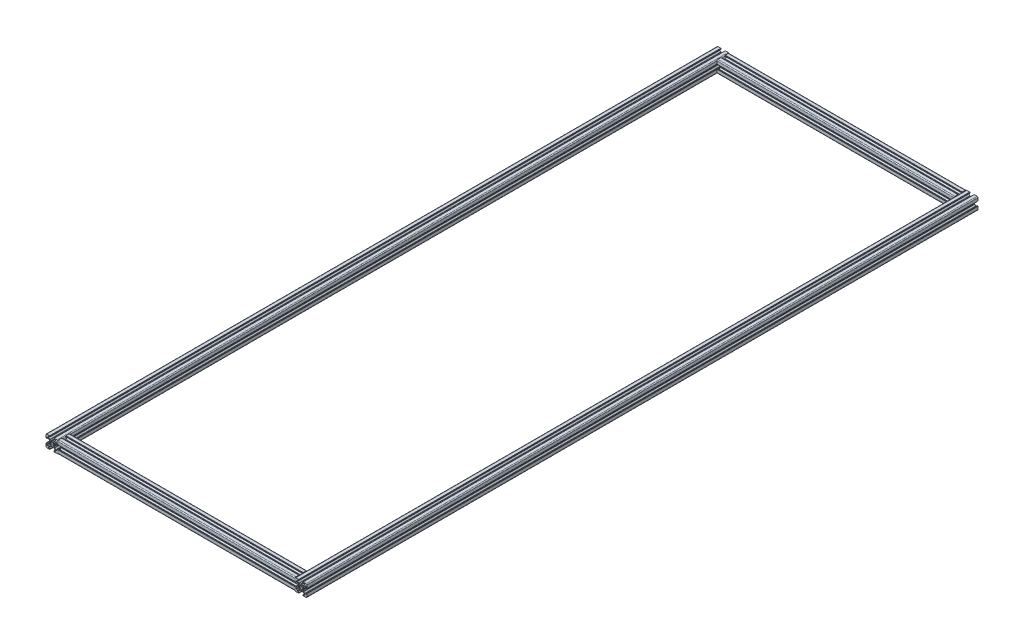
SolidWorks part; units mm, degrees
material "1060 Alloy"
ref_plane "Front Plane" through (0, 0, 0) normal (0, 0, 1) x (1, 0, 0)
ref_plane "Top Plane" through (0, 0, 0) normal (0, 1, 0) x (1, 0, 0)
ref_plane "Right Plane" through (0, 0, 0) normal (1, 0, 0) x (0, 0, -1)
sketch "Sketch1" plane through (0, 0, 0) normal (0, 1, 0) x (1, 0, 0)
  line L0 (0, -491.0294) -> (0, 633.9706)
  line L2 (417.4, -491.0294) -> (417.4, 633.9706)
  dimension "D1" = 1125
  dimension "D2" = 417.4
other "T-slot 20X20(1)"
ref_plane "Plane1" through (0, 0, 491.0294) normal (0, 0, -1) x (-1, 0, 0)
sketch "Sketch11" plane through (0, 0, 491.0294) normal (0, 0, -1) x (-1, 0, 0)
  line L0 (2.9914, 1.9095) -> (2.4445, 1.2578)
  line L1 (2.4445, -1.2578) -> (2.9914, -1.9095)
  line L2 (1.9134, -2.9889) -> (1.2578, -2.4445)
  line L3 (-1.2578, -2.4445) -> (-1.9135, -2.9889)
  line L4 (-2.9914, -1.9095) -> (-2.4445, -1.2578)
  line L5 (-2.4445, 1.2578) -> (-2.9914, 1.9095)
  line L6 (-1.9134, 2.9889) -> (-1.2578, 2.4445)
  line L7 (1.2577, 2.4446) -> (1.9134, 2.9889)
  line L8 (5.4998, -8.4985) -> (3.4998, -8.4985)
  line L9 (2.9998, -8.9985) -> (2.9998, -9.2985)
  line L10 (3.1998, -9.4985) -> (3.3489, -9.4985)
  line L11 (3.5489, -9.6985) -> (3.5489, -9.7989)
  line L12 (3.7489, -9.9989) -> (8.5002, -9.9989)
  line L13 (10.0002, -8.4989) -> (10.0002, -3.7489)
  line L14 (9.8002, -3.5489) -> (9.6994, -3.5489)
  line L15 (9.4994, -3.3489) -> (9.4994, -3.1985)
  line L16 (9.2994, -2.9985) -> (8.9994, -2.9985)
  line L17 (8.4994, -3.4985) -> (8.4994, -5.4986)
  line L18 (7.9994, -5.9986) -> (7.2672, -5.9986)
  line L19 (6.9136, -5.8521) -> (4.6458, -3.5844)
  line L20 (4.4994, -3.2308) -> (4.4994, -0.9522)
  line L21 (4.4726, -0.8522) -> (4.0375, -0.0986)
  line L22 (4.0375, 0.1014) -> (4.4726, 0.855)
  line L23 (4.4994, 0.955) -> (4.4994, 3.2333)
  line L24 (4.6458, 3.5869) -> (6.9136, 5.8546)
  line L25 (7.2672, 6.0011) -> (7.9994, 6.0011)
  line L26 (8.4994, 5.5011) -> (8.4994, 3.5007)
  line L27 (8.9994, 3.0007) -> (9.2994, 3.0007)
  line L28 (9.4994, 3.2007) -> (9.4994, 3.3489)
  line L29 (9.6994, 3.5489) -> (9.8002, 3.5489)
  line L30 (10.0002, 3.7489) -> (10.0002, 8.4989)
  line L31 (8.5002, 9.9989) -> (3.7489, 9.9989)
  line L32 (3.5489, 9.7989) -> (3.5489, 9.7011)
  line L33 (3.3489, 9.5011) -> (3.1998, 9.5011)
  line L34 (2.9998, 9.3011) -> (2.9998, 9.0011)
  line L35 (3.4998, 8.5011) -> (5.4998, 8.5011)
  line L36 (5.9998, 8.0011) -> (5.9998, 7.2692)
  line L37 (5.8533, 6.9156) -> (3.5852, 4.6475)
  line L38 (3.2317, 4.5011) -> (0.953, 4.5011)
  line L39 (0.853, 4.4743) -> (0.0994, 4.0392)
  line L40 (-0.1006, 4.0392) -> (-0.8542, 4.4743)
  line L41 (-0.9542, 4.5011) -> (-3.2325, 4.5011)
  line L42 (-3.586, 4.6475) -> (-5.8541, 6.9157)
  line L43 (-6.0006, 7.2692) -> (-6.0006, 8.0011)
  line L44 (-5.5006, 8.5011) -> (-3.5002, 8.5011)
  line L45 (-3.0002, 9.0011) -> (-3.0002, 9.3011)
  line L46 (-3.2002, 9.5011) -> (-3.3489, 9.5011)
  line L47 (-3.5489, 9.7011) -> (-3.5489, 9.7989)
  line L48 (-3.7489, 9.9989) -> (-8.4985, 9.9989)
  line L49 (-9.9985, 8.4989) -> (-9.9985, 3.7489)
  line L50 (-9.7985, 3.5489) -> (-9.6999, 3.5489)
  line L51 (-9.4999, 3.3489) -> (-9.4999, 3.2007)
  line L52 (-9.2999, 3.0007) -> (-8.9999, 3.0007)
  line L53 (-8.4999, 3.5007) -> (-8.4999, 5.5011)
  line L54 (-7.9999, 6.0011) -> (-7.2679, 6.0011)
  line L55 (-6.9144, 5.8546) -> (-4.6467, 3.5869)
  line L56 (-4.5003, 3.2334) -> (-4.5003, 0.955)
  line L57 (-4.4735, 0.855) -> (-4.0384, 0.1014)
  line L58 (-4.0384, -0.0986) -> (-4.4735, -0.8522)
  line L59 (-4.5003, -0.9522) -> (-4.5003, -3.2308)
  line L60 (-4.6467, -3.5844) -> (-6.9145, -5.8521)
  line L61 (-7.268, -5.9986) -> (-7.9999, -5.9986)
  line L62 (-8.4999, -5.4986) -> (-8.4999, -3.4985)
  line L63 (-8.9999, -2.9985) -> (-9.2999, -2.9985)
  line L64 (-9.4999, -3.1985) -> (-9.4999, -3.3489)
  line L65 (-9.6999, -3.5489) -> (-9.7985, -3.5489)
  line L66 (-9.9985, -3.7489) -> (-9.9985, -8.4989)
  line L67 (-8.4985, -9.9989) -> (-3.7489, -9.9989)
  line L68 (-3.5489, -9.7989) -> (-3.5489, -9.6985)
  line L69 (-3.3489, -9.4985) -> (-3.2002, -9.4985)
  line L70 (-3.0002, -9.2985) -> (-3.0002, -8.9985)
  line L71 (-3.5002, -8.4985) -> (-5.5006, -8.4985)
  line L72 (-6.0006, -7.9985) -> (-6.0006, -7.2667)
  line L73 (-5.8541, -6.9131) -> (-3.5864, -4.6454)
  line L74 (-3.2328, -4.4989) -> (-0.9542, -4.4989)
  line L75 (-0.8542, -4.4721) -> (-0.1006, -4.037)
  line L76 (0.0994, -4.037) -> (0.853, -4.4721)
  line L77 (0.953, -4.4989) -> (3.232, -4.4989)
  line L78 (3.5856, -4.6454) -> (5.8533, -6.9131)
  line L79 (5.9998, -7.2667) -> (5.9998, -7.9985)
  arc A0 (2.4445, 1.2578) -> (2.4445, -1.2578) centre (0, 0) cw
  arc A1 (2.9914, -1.9095) -> (1.9134, -2.9889) centre (0, 0) cw
  arc A2 (1.2578, -2.4445) -> (-1.2578, -2.4445) centre (0, 0) cw
  arc A3 (-1.9135, -2.9889) -> (-2.9914, -1.9095) centre (0, 0) cw
  arc A4 (-2.4445, -1.2578) -> (-2.4445, 1.2578) centre (0, 0) cw
  arc A5 (-2.9914, 1.9095) -> (-1.9134, 2.9889) centre (0, 0) cw
  arc A6 (-1.2578, 2.4445) -> (1.2577, 2.4446) centre (0, 0) cw
  arc A7 (1.9134, 2.9889) -> (2.9914, 1.9095) centre (0, 0) cw
  arc A8 (5.9998, -7.9985) -> (5.4998, -8.4985) centre (5.4998, -7.9985) cw
  arc A9 (3.4998, -8.4985) -> (2.9998, -8.9985) centre (3.4998, -8.9985) ccw
  arc A10 (2.9998, -9.2985) -> (3.1998, -9.4985) centre (3.1998, -9.2985) ccw
  arc A11 (3.3489, -9.4985) -> (3.5489, -9.6985) centre (3.3489, -9.6985) cw
  arc A12 (3.5489, -9.7989) -> (3.7489, -9.9989) centre (3.7489, -9.7989) ccw
  arc A13 (8.5002, -9.9989) -> (10.0002, -8.4989) centre (8.5002, -8.4989) ccw
  arc A14 (10.0002, -3.7489) -> (9.8002, -3.5489) centre (9.8002, -3.7489) ccw
  arc A15 (9.6994, -3.5489) -> (9.4994, -3.3489) centre (9.6994, -3.3489) cw
  arc A16 (9.4994, -3.1985) -> (9.2994, -2.9985) centre (9.2994, -3.1985) ccw
  arc A17 (8.9994, -2.9985) -> (8.4994, -3.4985) centre (8.9994, -3.4985) ccw
  arc A18 (8.4994, -5.4986) -> (7.9994, -5.9986) centre (7.9994, -5.4986) cw
  arc A19 (7.2672, -5.9986) -> (6.9136, -5.8521) centre (7.2672, -5.4986) cw
  arc A20 (4.6458, -3.5844) -> (4.4994, -3.2308) centre (4.9994, -3.2308) cw
  arc A21 (4.4994, -0.9522) -> (4.4726, -0.8522) centre (4.2994, -0.9522) ccw
  arc A22 (4.0375, -0.0986) -> (4.0375, 0.1014) centre (4.2107, 0.0014) cw
  arc A23 (4.4726, 0.855) -> (4.4994, 0.955) centre (4.2994, 0.955) ccw
  arc A24 (4.4994, 3.2333) -> (4.6458, 3.5869) centre (4.9994, 3.2333) cw
  arc A25 (6.9136, 5.8546) -> (7.2672, 6.0011) centre (7.2672, 5.5011) cw
  arc A26 (7.9994, 6.0011) -> (8.4994, 5.5011) centre (7.9994, 5.5011) cw
  arc A27 (8.4994, 3.5007) -> (8.9994, 3.0007) centre (8.9994, 3.5007) ccw
  arc A28 (9.2994, 3.0007) -> (9.4994, 3.2007) centre (9.2994, 3.2007) ccw
  arc A29 (9.4994, 3.3489) -> (9.6994, 3.5489) centre (9.6994, 3.3489) cw
  arc A30 (9.8002, 3.5489) -> (10.0002, 3.7489) centre (9.8002, 3.7489) ccw
  arc A31 (10.0002, 8.4989) -> (8.5002, 9.9989) centre (8.5002, 8.4989) ccw
  arc A32 (3.7489, 9.9989) -> (3.5489, 9.7989) centre (3.7489, 9.7989) ccw
  arc A33 (3.5489, 9.7011) -> (3.3489, 9.5011) centre (3.3489, 9.7011) cw
  arc A34 (3.1998, 9.5011) -> (2.9998, 9.3011) centre (3.1998, 9.3011) ccw
  arc A35 (2.9998, 9.0011) -> (3.4998, 8.5011) centre (3.4998, 9.0011) ccw
  arc A36 (5.4998, 8.5011) -> (5.9998, 8.0011) centre (5.4998, 8.0011) cw
  arc A37 (5.9998, 7.2692) -> (5.8533, 6.9156) centre (5.4998, 7.2692) cw
  arc A38 (3.5852, 4.6475) -> (3.2317, 4.5011) centre (3.2317, 5.0011) cw
  arc A39 (0.953, 4.5011) -> (0.853, 4.4743) centre (0.953, 4.3011) ccw
  arc A40 (0.0994, 4.0392) -> (-0.1006, 4.0392) centre (-0.0006, 4.2124) cw
  arc A41 (-0.8542, 4.4743) -> (-0.9542, 4.5011) centre (-0.9542, 4.3011) ccw
  arc A42 (-3.2325, 4.5011) -> (-3.586, 4.6475) centre (-3.2325, 5.0011) cw
  arc A43 (-5.8541, 6.9157) -> (-6.0006, 7.2692) centre (-5.5006, 7.2692) cw
  arc A44 (-6.0006, 8.0011) -> (-5.5006, 8.5011) centre (-5.5006, 8.0011) cw
  arc A45 (-3.5002, 8.5011) -> (-3.0002, 9.0011) centre (-3.5002, 9.0011) ccw
  arc A46 (-3.0002, 9.3011) -> (-3.2002, 9.5011) centre (-3.2002, 9.3011) ccw
  arc A47 (-3.3489, 9.5011) -> (-3.5489, 9.7011) centre (-3.3489, 9.7011) cw
  arc A48 (-3.5489, 9.7989) -> (-3.7489, 9.9989) centre (-3.7489, 9.7989) ccw
  arc A49 (-8.4985, 9.9989) -> (-9.9985, 8.4989) centre (-8.4985, 8.4989) ccw
  arc A50 (-9.9985, 3.7489) -> (-9.7985, 3.5489) centre (-9.7985, 3.7489) ccw
  arc A51 (-9.6999, 3.5489) -> (-9.4999, 3.3489) centre (-9.6999, 3.3489) cw
  arc A52 (-9.4999, 3.2007) -> (-9.2999, 3.0007) centre (-9.2999, 3.2007) ccw
  arc A53 (-8.9999, 3.0007) -> (-8.4999, 3.5007) centre (-8.9999, 3.5007) ccw
  arc A54 (-8.4999, 5.5011) -> (-7.9999, 6.0011) centre (-7.9999, 5.5011) cw
  arc A55 (-7.2679, 6.0011) -> (-6.9144, 5.8546) centre (-7.2679, 5.5011) cw
  arc A56 (-4.6467, 3.5869) -> (-4.5003, 3.2334) centre (-5.0003, 3.2334) cw
  arc A57 (-4.5003, 0.955) -> (-4.4735, 0.855) centre (-4.3003, 0.955) ccw
  arc A58 (-4.0384, 0.1014) -> (-4.0384, -0.0986) centre (-4.2116, 0.0014) cw
  arc A59 (-4.4735, -0.8522) -> (-4.5003, -0.9522) centre (-4.3003, -0.9522) ccw
  arc A60 (-4.5003, -3.2308) -> (-4.6467, -3.5844) centre (-5.0003, -3.2308) cw
  arc A61 (-6.9145, -5.8521) -> (-7.268, -5.9986) centre (-7.268, -5.4986) cw
  arc A62 (-7.9999, -5.9986) -> (-8.4999, -5.4986) centre (-7.9999, -5.4986) cw
  arc A63 (-8.4999, -3.4985) -> (-8.9999, -2.9985) centre (-8.9999, -3.4985) ccw
  arc A64 (-9.2999, -2.9985) -> (-9.4999, -3.1985) centre (-9.2999, -3.1985) ccw
  arc A65 (-9.4999, -3.3489) -> (-9.6999, -3.5489) centre (-9.6999, -3.3489) cw
  arc A66 (-9.7985, -3.5489) -> (-9.9985, -3.7489) centre (-9.7985, -3.7489) ccw
  arc A67 (-9.9985, -8.4989) -> (-8.4985, -9.9989) centre (-8.4985, -8.4989) ccw
  arc A68 (-3.7489, -9.9989) -> (-3.5489, -9.7989) centre (-3.7489, -9.7989) ccw
  arc A69 (-3.5489, -9.6985) -> (-3.3489, -9.4985) centre (-3.3489, -9.6985) cw
  arc A70 (-3.2002, -9.4985) -> (-3.0002, -9.2985) centre (-3.2002, -9.2985) ccw
  arc A71 (-3.0002, -8.9985) -> (-3.5002, -8.4985) centre (-3.5002, -8.9985) ccw
  arc A72 (-5.5006, -8.4985) -> (-6.0006, -7.9985) centre (-5.5006, -7.9985) cw
  arc A73 (-6.0006, -7.2667) -> (-5.8541, -6.9131) centre (-5.5006, -7.2667) cw
  arc A74 (-3.5864, -4.6454) -> (-3.2328, -4.4989) centre (-3.2328, -4.9989) cw
  arc A75 (-0.9542, -4.4989) -> (-0.8542, -4.4721) centre (-0.9542, -4.2989) ccw
  arc A76 (-0.1006, -4.037) -> (0.0994, -4.037) centre (-0.0006, -4.2102) cw
  arc A77 (0.853, -4.4721) -> (0.953, -4.4989) centre (0.953, -4.2989) ccw
  arc A78 (3.232, -4.4989) -> (3.5856, -4.6454) centre (3.232, -4.9989) cw
  arc A79 (5.8533, -6.9131) -> (5.9998, -7.2667) centre (5.4998, -7.2667) cw
  point P233 (0, 0)
sketch "Sketch12" plane through (0, 0, 0) normal (0, 1, 0) x (1, 0, 0)
  line L0 (9.9985, 633.9706) -> (9.9985, -491.0294) construction
  line L1 (9.9985, 623.9706) -> (407.3998, 623.9706)
  line L2 (407.3998, 633.9706) -> (407.3998, -491.0294) construction
  point P0 (9.9985, 623.9706)
  dimension "D1" = 10
other "T-slot 20X20(2)"
ref_plane "Plane2" through (9.9985, 0, -623.9706) normal (1, 0, 0) x (0, 0, -1)
sketch "Sketch13" plane through (9.9985, 0, -623.9706) normal (1, 0, 0) x (0, 0, -1)
  line L0 (2.9914, 1.9095) -> (2.4445, 1.2578)
  line L1 (2.4445, -1.2578) -> (2.9914, -1.9095)
  line L2 (1.9134, -2.9889) -> (1.2578, -2.4445)
  line L3 (-1.2578, -2.4445) -> (-1.9135, -2.9889)
  line L4 (-2.9914, -1.9095) -> (-2.4445, -1.2578)
  line L5 (-2.4445, 1.2578) -> (-2.9914, 1.9095)
  line L6 (-1.9134, 2.9889) -> (-1.2578, 2.4445)
  line L7 (1.2577, 2.4446) -> (1.9134, 2.9889)
  line L8 (5.4998, -8.4985) -> (3.4998, -8.4985)
  line L9 (2.9998, -8.9985) -> (2.9998, -9.2985)
  line L10 (3.1998, -9.4985) -> (3.3489, -9.4985)
  line L11 (3.5489, -9.6985) -> (3.5489, -9.7989)
  line L12 (3.7489, -9.9989) -> (8.5002, -9.9989)
  line L13 (10.0002, -8.4989) -> (10.0002, -3.7489)
  line L14 (9.8002, -3.5489) -> (9.6994, -3.5489)
  line L15 (9.4994, -3.3489) -> (9.4994, -3.1985)
  line L16 (9.2994, -2.9985) -> (8.9994, -2.9985)
  line L17 (8.4994, -3.4985) -> (8.4994, -5.4986)
  line L18 (7.9994, -5.9986) -> (7.2672, -5.9986)
  line L19 (6.9136, -5.8521) -> (4.6458, -3.5844)
  line L20 (4.4994, -3.2308) -> (4.4994, -0.9522)
  line L21 (4.4726, -0.8522) -> (4.0375, -0.0986)
  line L22 (4.0375, 0.1014) -> (4.4726, 0.855)
  line L23 (4.4994, 0.955) -> (4.4994, 3.2333)
  line L24 (4.6458, 3.5869) -> (6.9136, 5.8546)
  line L25 (7.2672, 6.0011) -> (7.9994, 6.0011)
  line L26 (8.4994, 5.5011) -> (8.4994, 3.5007)
  line L27 (8.9994, 3.0007) -> (9.2994, 3.0007)
  line L28 (9.4994, 3.2007) -> (9.4994, 3.3489)
  line L29 (9.6994, 3.5489) -> (9.8002, 3.5489)
  line L30 (10.0002, 3.7489) -> (10.0002, 8.4989)
  line L31 (8.5002, 9.9989) -> (3.7489, 9.9989)
  line L32 (3.5489, 9.7989) -> (3.5489, 9.7011)
  line L33 (3.3489, 9.5011) -> (3.1998, 9.5011)
  line L34 (2.9998, 9.3011) -> (2.9998, 9.0011)
  line L35 (3.4998, 8.5011) -> (5.4998, 8.5011)
  line L36 (5.9998, 8.0011) -> (5.9998, 7.2692)
  line L37 (5.8533, 6.9156) -> (3.5852, 4.6475)
  line L38 (3.2317, 4.5011) -> (0.953, 4.5011)
  line L39 (0.853, 4.4743) -> (0.0994, 4.0392)
  line L40 (-0.1006, 4.0392) -> (-0.8542, 4.4743)
  line L41 (-0.9542, 4.5011) -> (-3.2325, 4.5011)
  line L42 (-3.586, 4.6475) -> (-5.8541, 6.9157)
  line L43 (-6.0006, 7.2692) -> (-6.0006, 8.0011)
  line L44 (-5.5006, 8.5011) -> (-3.5002, 8.5011)
  line L45 (-3.0002, 9.0011) -> (-3.0002, 9.3011)
  line L46 (-3.2002, 9.5011) -> (-3.3489, 9.5011)
  line L47 (-3.5489, 9.7011) -> (-3.5489, 9.7989)
  line L48 (-3.7489, 9.9989) -> (-8.4985, 9.9989)
  line L49 (-9.9985, 8.4989) -> (-9.9985, 3.7489)
  line L50 (-9.7985, 3.5489) -> (-9.6999, 3.5489)
  line L51 (-9.4999, 3.3489) -> (-9.4999, 3.2007)
  line L52 (-9.2999, 3.0007) -> (-8.9999, 3.0007)
  line L53 (-8.4999, 3.5007) -> (-8.4999, 5.5011)
  line L54 (-7.9999, 6.0011) -> (-7.2679, 6.0011)
  line L55 (-6.9144, 5.8546) -> (-4.6467, 3.5869)
  line L56 (-4.5003, 3.2334) -> (-4.5003, 0.955)
  line L57 (-4.4735, 0.855) -> (-4.0384, 0.1014)
  line L58 (-4.0384, -0.0986) -> (-4.4735, -0.8522)
  line L59 (-4.5003, -0.9522) -> (-4.5003, -3.2308)
  line L60 (-4.6467, -3.5844) -> (-6.9145, -5.8521)
  line L61 (-7.268, -5.9986) -> (-7.9999, -5.9986)
  line L62 (-8.4999, -5.4986) -> (-8.4999, -3.4985)
  line L63 (-8.9999, -2.9985) -> (-9.2999, -2.9985)
  line L64 (-9.4999, -3.1985) -> (-9.4999, -3.3489)
  line L65 (-9.6999, -3.5489) -> (-9.7985, -3.5489)
  line L66 (-9.9985, -3.7489) -> (-9.9985, -8.4989)
  line L67 (-8.4985, -9.9989) -> (-3.7489, -9.9989)
  line L68 (-3.5489, -9.7989) -> (-3.5489, -9.6985)
  line L69 (-3.3489, -9.4985) -> (-3.2002, -9.4985)
  line L70 (-3.0002, -9.2985) -> (-3.0002, -8.9985)
  line L71 (-3.5002, -8.4985) -> (-5.5006, -8.4985)
  line L72 (-6.0006, -7.9985) -> (-6.0006, -7.2667)
  line L73 (-5.8541, -6.9131) -> (-3.5864, -4.6454)
  line L74 (-3.2328, -4.4989) -> (-0.9542, -4.4989)
  line L75 (-0.8542, -4.4721) -> (-0.1006, -4.037)
  line L76 (0.0994, -4.037) -> (0.853, -4.4721)
  line L77 (0.953, -4.4989) -> (3.232, -4.4989)
  line L78 (3.5856, -4.6454) -> (5.8533, -6.9131)
  line L79 (5.9998, -7.2667) -> (5.9998, -7.9985)
  arc A0 (2.4445, 1.2578) -> (2.4445, -1.2578) centre (0, 0) cw
  arc A1 (2.9914, -1.9095) -> (1.9134, -2.9889) centre (0, 0) cw
  arc A2 (1.2578, -2.4445) -> (-1.2578, -2.4445) centre (0, 0) cw
  arc A3 (-1.9135, -2.9889) -> (-2.9914, -1.9095) centre (0, 0) cw
  arc A4 (-2.4445, -1.2578) -> (-2.4445, 1.2578) centre (0, 0) cw
  arc A5 (-2.9914, 1.9095) -> (-1.9134, 2.9889) centre (0, 0) cw
  arc A6 (-1.2578, 2.4445) -> (1.2577, 2.4446) centre (0, 0) cw
  arc A7 (1.9134, 2.9889) -> (2.9914, 1.9095) centre (0, 0) cw
  arc A8 (5.9998, -7.9985) -> (5.4998, -8.4985) centre (5.4998, -7.9985) cw
  arc A9 (3.4998, -8.4985) -> (2.9998, -8.9985) centre (3.4998, -8.9985) ccw
  arc A10 (2.9998, -9.2985) -> (3.1998, -9.4985) centre (3.1998, -9.2985) ccw
  arc A11 (3.3489, -9.4985) -> (3.5489, -9.6985) centre (3.3489, -9.6985) cw
  arc A12 (3.5489, -9.7989) -> (3.7489, -9.9989) centre (3.7489, -9.7989) ccw
  arc A13 (8.5002, -9.9989) -> (10.0002, -8.4989) centre (8.5002, -8.4989) ccw
  arc A14 (10.0002, -3.7489) -> (9.8002, -3.5489) centre (9.8002, -3.7489) ccw
  arc A15 (9.6994, -3.5489) -> (9.4994, -3.3489) centre (9.6994, -3.3489) cw
  arc A16 (9.4994, -3.1985) -> (9.2994, -2.9985) centre (9.2994, -3.1985) ccw
  arc A17 (8.9994, -2.9985) -> (8.4994, -3.4985) centre (8.9994, -3.4985) ccw
  arc A18 (8.4994, -5.4986) -> (7.9994, -5.9986) centre (7.9994, -5.4986) cw
  arc A19 (7.2672, -5.9986) -> (6.9136, -5.8521) centre (7.2672, -5.4986) cw
  arc A20 (4.6458, -3.5844) -> (4.4994, -3.2308) centre (4.9994, -3.2308) cw
  arc A21 (4.4994, -0.9522) -> (4.4726, -0.8522) centre (4.2994, -0.9522) ccw
  arc A22 (4.0375, -0.0986) -> (4.0375, 0.1014) centre (4.2107, 0.0014) cw
  arc A23 (4.4726, 0.855) -> (4.4994, 0.955) centre (4.2994, 0.955) ccw
  arc A24 (4.4994, 3.2333) -> (4.6458, 3.5869) centre (4.9994, 3.2333) cw
  arc A25 (6.9136, 5.8546) -> (7.2672, 6.0011) centre (7.2672, 5.5011) cw
  arc A26 (7.9994, 6.0011) -> (8.4994, 5.5011) centre (7.9994, 5.5011) cw
  arc A27 (8.4994, 3.5007) -> (8.9994, 3.0007) centre (8.9994, 3.5007) ccw
  arc A28 (9.2994, 3.0007) -> (9.4994, 3.2007) centre (9.2994, 3.2007) ccw
  arc A29 (9.4994, 3.3489) -> (9.6994, 3.5489) centre (9.6994, 3.3489) cw
  arc A30 (9.8002, 3.5489) -> (10.0002, 3.7489) centre (9.8002, 3.7489) ccw
  arc A31 (10.0002, 8.4989) -> (8.5002, 9.9989) centre (8.5002, 8.4989) ccw
  arc A32 (3.7489, 9.9989) -> (3.5489, 9.7989) centre (3.7489, 9.7989) ccw
  arc A33 (3.5489, 9.7011) -> (3.3489, 9.5011) centre (3.3489, 9.7011) cw
  arc A34 (3.1998, 9.5011) -> (2.9998, 9.3011) centre (3.1998, 9.3011) ccw
  arc A35 (2.9998, 9.0011) -> (3.4998, 8.5011) centre (3.4998, 9.0011) ccw
  arc A36 (5.4998, 8.5011) -> (5.9998, 8.0011) centre (5.4998, 8.0011) cw
  arc A37 (5.9998, 7.2692) -> (5.8533, 6.9156) centre (5.4998, 7.2692) cw
  arc A38 (3.5852, 4.6475) -> (3.2317, 4.5011) centre (3.2317, 5.0011) cw
  arc A39 (0.953, 4.5011) -> (0.853, 4.4743) centre (0.953, 4.3011) ccw
  arc A40 (0.0994, 4.0392) -> (-0.1006, 4.0392) centre (-0.0006, 4.2124) cw
  arc A41 (-0.8542, 4.4743) -> (-0.9542, 4.5011) centre (-0.9542, 4.3011) ccw
  arc A42 (-3.2325, 4.5011) -> (-3.586, 4.6475) centre (-3.2325, 5.0011) cw
  arc A43 (-5.8541, 6.9157) -> (-6.0006, 7.2692) centre (-5.5006, 7.2692) cw
  arc A44 (-6.0006, 8.0011) -> (-5.5006, 8.5011) centre (-5.5006, 8.0011) cw
  arc A45 (-3.5002, 8.5011) -> (-3.0002, 9.0011) centre (-3.5002, 9.0011) ccw
  arc A46 (-3.0002, 9.3011) -> (-3.2002, 9.5011) centre (-3.2002, 9.3011) ccw
  arc A47 (-3.3489, 9.5011) -> (-3.5489, 9.7011) centre (-3.3489, 9.7011) cw
  arc A48 (-3.5489, 9.7989) -> (-3.7489, 9.9989) centre (-3.7489, 9.7989) ccw
  arc A49 (-8.4985, 9.9989) -> (-9.9985, 8.4989) centre (-8.4985, 8.4989) ccw
  arc A50 (-9.9985, 3.7489) -> (-9.7985, 3.5489) centre (-9.7985, 3.7489) ccw
  arc A51 (-9.6999, 3.5489) -> (-9.4999, 3.3489) centre (-9.6999, 3.3489) cw
  arc A52 (-9.4999, 3.2007) -> (-9.2999, 3.0007) centre (-9.2999, 3.2007) ccw
  arc A53 (-8.9999, 3.0007) -> (-8.4999, 3.5007) centre (-8.9999, 3.5007) ccw
  arc A54 (-8.4999, 5.5011) -> (-7.9999, 6.0011) centre (-7.9999, 5.5011) cw
  arc A55 (-7.2679, 6.0011) -> (-6.9144, 5.8546) centre (-7.2679, 5.5011) cw
  arc A56 (-4.6467, 3.5869) -> (-4.5003, 3.2334) centre (-5.0003, 3.2334) cw
  arc A57 (-4.5003, 0.955) -> (-4.4735, 0.855) centre (-4.3003, 0.955) ccw
  arc A58 (-4.0384, 0.1014) -> (-4.0384, -0.0986) centre (-4.2116, 0.0014) cw
  arc A59 (-4.4735, -0.8522) -> (-4.5003, -0.9522) centre (-4.3003, -0.9522) ccw
  arc A60 (-4.5003, -3.2308) -> (-4.6467, -3.5844) centre (-5.0003, -3.2308) cw
  arc A61 (-6.9145, -5.8521) -> (-7.268, -5.9986) centre (-7.268, -5.4986) cw
  arc A62 (-7.9999, -5.9986) -> (-8.4999, -5.4986) centre (-7.9999, -5.4986) cw
  arc A63 (-8.4999, -3.4985) -> (-8.9999, -2.9985) centre (-8.9999, -3.4985) ccw
  arc A64 (-9.2999, -2.9985) -> (-9.4999, -3.1985) centre (-9.2999, -3.1985) ccw
  arc A65 (-9.4999, -3.3489) -> (-9.6999, -3.5489) centre (-9.6999, -3.3489) cw
  arc A66 (-9.7985, -3.5489) -> (-9.9985, -3.7489) centre (-9.7985, -3.7489) ccw
  arc A67 (-9.9985, -8.4989) -> (-8.4985, -9.9989) centre (-8.4985, -8.4989) ccw
  arc A68 (-3.7489, -9.9989) -> (-3.5489, -9.7989) centre (-3.7489, -9.7989) ccw
  arc A69 (-3.5489, -9.6985) -> (-3.3489, -9.4985) centre (-3.3489, -9.6985) cw
  arc A70 (-3.2002, -9.4985) -> (-3.0002, -9.2985) centre (-3.2002, -9.2985) ccw
  arc A71 (-3.0002, -8.9985) -> (-3.5002, -8.4985) centre (-3.5002, -8.9985) ccw
  arc A72 (-5.5006, -8.4985) -> (-6.0006, -7.9985) centre (-5.5006, -7.9985) cw
  arc A73 (-6.0006, -7.2667) -> (-5.8541, -6.9131) centre (-5.5006, -7.2667) cw
  arc A74 (-3.5864, -4.6454) -> (-3.2328, -4.4989) centre (-3.2328, -4.9989) cw
  arc A75 (-0.9542, -4.4989) -> (-0.8542, -4.4721) centre (-0.9542, -4.2989) ccw
  arc A76 (-0.1006, -4.037) -> (0.0994, -4.037) centre (-0.0006, -4.2102) cw
  arc A77 (0.853, -4.4721) -> (0.953, -4.4989) centre (0.953, -4.2989) ccw
  arc A78 (3.232, -4.4989) -> (3.5856, -4.6454) centre (3.232, -4.9989) cw
  arc A79 (5.8533, -6.9131) -> (5.9998, -7.2667) centre (5.4998, -7.2667) cw
  point P233 (0, 0)
sketch "Sketch14" plane through (0, 0, 0) normal (0, 1, 0) x (1, 0, 0)
  line L0 (9.9027, -481.0294) -> (407.3998, -481.0294)
  line L1 (407.3998, 633.9706) -> (407.3998, -491.0294) construction
  point P0 (9.9027, -481.0294)
  dimension "D1" = 10
other "T-slot 20X20(3)"
ref_plane "Plane3" through (9.9027, 0, 481.0294) normal (1, 0, 0) x (0, 0, -1)
sketch "Sketch15" plane through (9.9027, 0, 481.0294) normal (1, 0, 0) x (0, 0, -1)
  line L0 (2.9914, 1.9095) -> (2.4445, 1.2578)
  line L1 (2.4445, -1.2578) -> (2.9914, -1.9095)
  line L2 (1.9134, -2.9889) -> (1.2578, -2.4445)
  line L3 (-1.2578, -2.4445) -> (-1.9135, -2.9889)
  line L4 (-2.9914, -1.9095) -> (-2.4445, -1.2578)
  line L5 (-2.4445, 1.2578) -> (-2.9914, 1.9095)
  line L6 (-1.9134, 2.9889) -> (-1.2578, 2.4445)
  line L7 (1.2577, 2.4446) -> (1.9134, 2.9889)
  line L8 (5.4998, -8.4985) -> (3.4998, -8.4985)
  line L9 (2.9998, -8.9985) -> (2.9998, -9.2985)
  line L10 (3.1998, -9.4985) -> (3.3489, -9.4985)
  line L11 (3.5489, -9.6985) -> (3.5489, -9.7989)
  line L12 (3.7489, -9.9989) -> (8.5002, -9.9989)
  line L13 (10.0002, -8.4989) -> (10.0002, -3.7489)
  line L14 (9.8002, -3.5489) -> (9.6994, -3.5489)
  line L15 (9.4994, -3.3489) -> (9.4994, -3.1985)
  line L16 (9.2994, -2.9985) -> (8.9994, -2.9985)
  line L17 (8.4994, -3.4985) -> (8.4994, -5.4986)
  line L18 (7.9994, -5.9986) -> (7.2672, -5.9986)
  line L19 (6.9136, -5.8521) -> (4.6458, -3.5844)
  line L20 (4.4994, -3.2308) -> (4.4994, -0.9522)
  line L21 (4.4726, -0.8522) -> (4.0375, -0.0986)
  line L22 (4.0375, 0.1014) -> (4.4726, 0.855)
  line L23 (4.4994, 0.955) -> (4.4994, 3.2333)
  line L24 (4.6458, 3.5869) -> (6.9136, 5.8546)
  line L25 (7.2672, 6.0011) -> (7.9994, 6.0011)
  line L26 (8.4994, 5.5011) -> (8.4994, 3.5007)
  line L27 (8.9994, 3.0007) -> (9.2994, 3.0007)
  line L28 (9.4994, 3.2007) -> (9.4994, 3.3489)
  line L29 (9.6994, 3.5489) -> (9.8002, 3.5489)
  line L30 (10.0002, 3.7489) -> (10.0002, 8.4989)
  line L31 (8.5002, 9.9989) -> (3.7489, 9.9989)
  line L32 (3.5489, 9.7989) -> (3.5489, 9.7011)
  line L33 (3.3489, 9.5011) -> (3.1998, 9.5011)
  line L34 (2.9998, 9.3011) -> (2.9998, 9.0011)
  line L35 (3.4998, 8.5011) -> (5.4998, 8.5011)
  line L36 (5.9998, 8.0011) -> (5.9998, 7.2692)
  line L37 (5.8533, 6.9156) -> (3.5852, 4.6475)
  line L38 (3.2317, 4.5011) -> (0.953, 4.5011)
  line L39 (0.853, 4.4743) -> (0.0994, 4.0392)
  line L40 (-0.1006, 4.0392) -> (-0.8542, 4.4743)
  line L41 (-0.9542, 4.5011) -> (-3.2325, 4.5011)
  line L42 (-3.586, 4.6475) -> (-5.8541, 6.9157)
  line L43 (-6.0006, 7.2692) -> (-6.0006, 8.0011)
  line L44 (-5.5006, 8.5011) -> (-3.5002, 8.5011)
  line L45 (-3.0002, 9.0011) -> (-3.0002, 9.3011)
  line L46 (-3.2002, 9.5011) -> (-3.3489, 9.5011)
  line L47 (-3.5489, 9.7011) -> (-3.5489, 9.7989)
  line L48 (-3.7489, 9.9989) -> (-8.4985, 9.9989)
  line L49 (-9.9985, 8.4989) -> (-9.9985, 3.7489)
  line L50 (-9.7985, 3.5489) -> (-9.6999, 3.5489)
  line L51 (-9.4999, 3.3489) -> (-9.4999, 3.2007)
  line L52 (-9.2999, 3.0007) -> (-8.9999, 3.0007)
  line L53 (-8.4999, 3.5007) -> (-8.4999, 5.5011)
  line L54 (-7.9999, 6.0011) -> (-7.2679, 6.0011)
  line L55 (-6.9144, 5.8546) -> (-4.6467, 3.5869)
  line L56 (-4.5003, 3.2334) -> (-4.5003, 0.955)
  line L57 (-4.4735, 0.855) -> (-4.0384, 0.1014)
  line L58 (-4.0384, -0.0986) -> (-4.4735, -0.8522)
  line L59 (-4.5003, -0.9522) -> (-4.5003, -3.2308)
  line L60 (-4.6467, -3.5844) -> (-6.9145, -5.8521)
  line L61 (-7.268, -5.9986) -> (-7.9999, -5.9986)
  line L62 (-8.4999, -5.4986) -> (-8.4999, -3.4985)
  line L63 (-8.9999, -2.9985) -> (-9.2999, -2.9985)
  line L64 (-9.4999, -3.1985) -> (-9.4999, -3.3489)
  line L65 (-9.6999, -3.5489) -> (-9.7985, -3.5489)
  line L66 (-9.9985, -3.7489) -> (-9.9985, -8.4989)
  line L67 (-8.4985, -9.9989) -> (-3.7489, -9.9989)
  line L68 (-3.5489, -9.7989) -> (-3.5489, -9.6985)
  line L69 (-3.3489, -9.4985) -> (-3.2002, -9.4985)
  line L70 (-3.0002, -9.2985) -> (-3.0002, -8.9985)
  line L71 (-3.5002, -8.4985) -> (-5.5006, -8.4985)
  line L72 (-6.0006, -7.9985) -> (-6.0006, -7.2667)
  line L73 (-5.8541, -6.9131) -> (-3.5864, -4.6454)
  line L74 (-3.2328, -4.4989) -> (-0.9542, -4.4989)
  line L75 (-0.8542, -4.4721) -> (-0.1006, -4.037)
  line L76 (0.0994, -4.037) -> (0.853, -4.4721)
  line L77 (0.953, -4.4989) -> (3.232, -4.4989)
  line L78 (3.5856, -4.6454) -> (5.8533, -6.9131)
  line L79 (5.9998, -7.2667) -> (5.9998, -7.9985)
  arc A0 (2.4445, 1.2578) -> (2.4445, -1.2578) centre (0, 0) cw
  arc A1 (2.9914, -1.9095) -> (1.9134, -2.9889) centre (0, 0) cw
  arc A2 (1.2578, -2.4445) -> (-1.2578, -2.4445) centre (0, 0) cw
  arc A3 (-1.9135, -2.9889) -> (-2.9914, -1.9095) centre (0, 0) cw
  arc A4 (-2.4445, -1.2578) -> (-2.4445, 1.2578) centre (0, 0) cw
  arc A5 (-2.9914, 1.9095) -> (-1.9134, 2.9889) centre (0, 0) cw
  arc A6 (-1.2578, 2.4445) -> (1.2577, 2.4446) centre (0, 0) cw
  arc A7 (1.9134, 2.9889) -> (2.9914, 1.9095) centre (0, 0) cw
  arc A8 (5.9998, -7.9985) -> (5.4998, -8.4985) centre (5.4998, -7.9985) cw
  arc A9 (3.4998, -8.4985) -> (2.9998, -8.9985) centre (3.4998, -8.9985) ccw
  arc A10 (2.9998, -9.2985) -> (3.1998, -9.4985) centre (3.1998, -9.2985) ccw
  arc A11 (3.3489, -9.4985) -> (3.5489, -9.6985) centre (3.3489, -9.6985) cw
  arc A12 (3.5489, -9.7989) -> (3.7489, -9.9989) centre (3.7489, -9.7989) ccw
  arc A13 (8.5002, -9.9989) -> (10.0002, -8.4989) centre (8.5002, -8.4989) ccw
  arc A14 (10.0002, -3.7489) -> (9.8002, -3.5489) centre (9.8002, -3.7489) ccw
  arc A15 (9.6994, -3.5489) -> (9.4994, -3.3489) centre (9.6994, -3.3489) cw
  arc A16 (9.4994, -3.1985) -> (9.2994, -2.9985) centre (9.2994, -3.1985) ccw
  arc A17 (8.9994, -2.9985) -> (8.4994, -3.4985) centre (8.9994, -3.4985) ccw
  arc A18 (8.4994, -5.4986) -> (7.9994, -5.9986) centre (7.9994, -5.4986) cw
  arc A19 (7.2672, -5.9986) -> (6.9136, -5.8521) centre (7.2672, -5.4986) cw
  arc A20 (4.6458, -3.5844) -> (4.4994, -3.2308) centre (4.9994, -3.2308) cw
  arc A21 (4.4994, -0.9522) -> (4.4726, -0.8522) centre (4.2994, -0.9522) ccw
  arc A22 (4.0375, -0.0986) -> (4.0375, 0.1014) centre (4.2107, 0.0014) cw
  arc A23 (4.4726, 0.855) -> (4.4994, 0.955) centre (4.2994, 0.955) ccw
  arc A24 (4.4994, 3.2333) -> (4.6458, 3.5869) centre (4.9994, 3.2333) cw
  arc A25 (6.9136, 5.8546) -> (7.2672, 6.0011) centre (7.2672, 5.5011) cw
  arc A26 (7.9994, 6.0011) -> (8.4994, 5.5011) centre (7.9994, 5.5011) cw
  arc A27 (8.4994, 3.5007) -> (8.9994, 3.0007) centre (8.9994, 3.5007) ccw
  arc A28 (9.2994, 3.0007) -> (9.4994, 3.2007) centre (9.2994, 3.2007) ccw
  arc A29 (9.4994, 3.3489) -> (9.6994, 3.5489) centre (9.6994, 3.3489) cw
  arc A30 (9.8002, 3.5489) -> (10.0002, 3.7489) centre (9.8002, 3.7489) ccw
  arc A31 (10.0002, 8.4989) -> (8.5002, 9.9989) centre (8.5002, 8.4989) ccw
  arc A32 (3.7489, 9.9989) -> (3.5489, 9.7989) centre (3.7489, 9.7989) ccw
  arc A33 (3.5489, 9.7011) -> (3.3489, 9.5011) centre (3.3489, 9.7011) cw
  arc A34 (3.1998, 9.5011) -> (2.9998, 9.3011) centre (3.1998, 9.3011) ccw
  arc A35 (2.9998, 9.0011) -> (3.4998, 8.5011) centre (3.4998, 9.0011) ccw
  arc A36 (5.4998, 8.5011) -> (5.9998, 8.0011) centre (5.4998, 8.0011) cw
  arc A37 (5.9998, 7.2692) -> (5.8533, 6.9156) centre (5.4998, 7.2692) cw
  arc A38 (3.5852, 4.6475) -> (3.2317, 4.5011) centre (3.2317, 5.0011) cw
  arc A39 (0.953, 4.5011) -> (0.853, 4.4743) centre (0.953, 4.3011) ccw
  arc A40 (0.0994, 4.0392) -> (-0.1006, 4.0392) centre (-0.0006, 4.2124) cw
  arc A41 (-0.8542, 4.4743) -> (-0.9542, 4.5011) centre (-0.9542, 4.3011) ccw
  arc A42 (-3.2325, 4.5011) -> (-3.586, 4.6475) centre (-3.2325, 5.0011) cw
  arc A43 (-5.8541, 6.9157) -> (-6.0006, 7.2692) centre (-5.5006, 7.2692) cw
  arc A44 (-6.0006, 8.0011) -> (-5.5006, 8.5011) centre (-5.5006, 8.0011) cw
  arc A45 (-3.5002, 8.5011) -> (-3.0002, 9.0011) centre (-3.5002, 9.0011) ccw
  arc A46 (-3.0002, 9.3011) -> (-3.2002, 9.5011) centre (-3.2002, 9.3011) ccw
  arc A47 (-3.3489, 9.5011) -> (-3.5489, 9.7011) centre (-3.3489, 9.7011) cw
  arc A48 (-3.5489, 9.7989) -> (-3.7489, 9.9989) centre (-3.7489, 9.7989) ccw
  arc A49 (-8.4985, 9.9989) -> (-9.9985, 8.4989) centre (-8.4985, 8.4989) ccw
  arc A50 (-9.9985, 3.7489) -> (-9.7985, 3.5489) centre (-9.7985, 3.7489) ccw
  arc A51 (-9.6999, 3.5489) -> (-9.4999, 3.3489) centre (-9.6999, 3.3489) cw
  arc A52 (-9.4999, 3.2007) -> (-9.2999, 3.0007) centre (-9.2999, 3.2007) ccw
  arc A53 (-8.9999, 3.0007) -> (-8.4999, 3.5007) centre (-8.9999, 3.5007) ccw
  arc A54 (-8.4999, 5.5011) -> (-7.9999, 6.0011) centre (-7.9999, 5.5011) cw
  arc A55 (-7.2679, 6.0011) -> (-6.9144, 5.8546) centre (-7.2679, 5.5011) cw
  arc A56 (-4.6467, 3.5869) -> (-4.5003, 3.2334) centre (-5.0003, 3.2334) cw
  arc A57 (-4.5003, 0.955) -> (-4.4735, 0.855) centre (-4.3003, 0.955) ccw
  arc A58 (-4.0384, 0.1014) -> (-4.0384, -0.0986) centre (-4.2116, 0.0014) cw
  arc A59 (-4.4735, -0.8522) -> (-4.5003, -0.9522) centre (-4.3003, -0.9522) ccw
  arc A60 (-4.5003, -3.2308) -> (-4.6467, -3.5844) centre (-5.0003, -3.2308) cw
  arc A61 (-6.9145, -5.8521) -> (-7.268, -5.9986) centre (-7.268, -5.4986) cw
  arc A62 (-7.9999, -5.9986) -> (-8.4999, -5.4986) centre (-7.9999, -5.4986) cw
  arc A63 (-8.4999, -3.4985) -> (-8.9999, -2.9985) centre (-8.9999, -3.4985) ccw
  arc A64 (-9.2999, -2.9985) -> (-9.4999, -3.1985) centre (-9.2999, -3.1985) ccw
  arc A65 (-9.4999, -3.3489) -> (-9.6999, -3.5489) centre (-9.6999, -3.3489) cw
  arc A66 (-9.7985, -3.5489) -> (-9.9985, -3.7489) centre (-9.7985, -3.7489) ccw
  arc A67 (-9.9985, -8.4989) -> (-8.4985, -9.9989) centre (-8.4985, -8.4989) ccw
  arc A68 (-3.7489, -9.9989) -> (-3.5489, -9.7989) centre (-3.7489, -9.7989) ccw
  arc A69 (-3.5489, -9.6985) -> (-3.3489, -9.4985) centre (-3.3489, -9.6985) cw
  arc A70 (-3.2002, -9.4985) -> (-3.0002, -9.2985) centre (-3.2002, -9.2985) ccw
  arc A71 (-3.0002, -8.9985) -> (-3.5002, -8.4985) centre (-3.5002, -8.9985) ccw
  arc A72 (-5.5006, -8.4985) -> (-6.0006, -7.9985) centre (-5.5006, -7.9985) cw
  arc A73 (-6.0006, -7.2667) -> (-5.8541, -6.9131) centre (-5.5006, -7.2667) cw
  arc A74 (-3.5864, -4.6454) -> (-3.2328, -4.4989) centre (-3.2328, -4.9989) cw
  arc A75 (-0.9542, -4.4989) -> (-0.8542, -4.4721) centre (-0.9542, -4.2989) ccw
  arc A76 (-0.1006, -4.037) -> (0.0994, -4.037) centre (-0.0006, -4.2102) cw
  arc A77 (0.853, -4.4721) -> (0.953, -4.4989) centre (0.953, -4.2989) ccw
  arc A78 (3.232, -4.4989) -> (3.5856, -4.6454) centre (3.232, -4.9989) cw
  arc A79 (5.8533, -6.9131) -> (5.9998, -7.2667) centre (5.4998, -7.2667) cw
  point P233 (0, 0)
